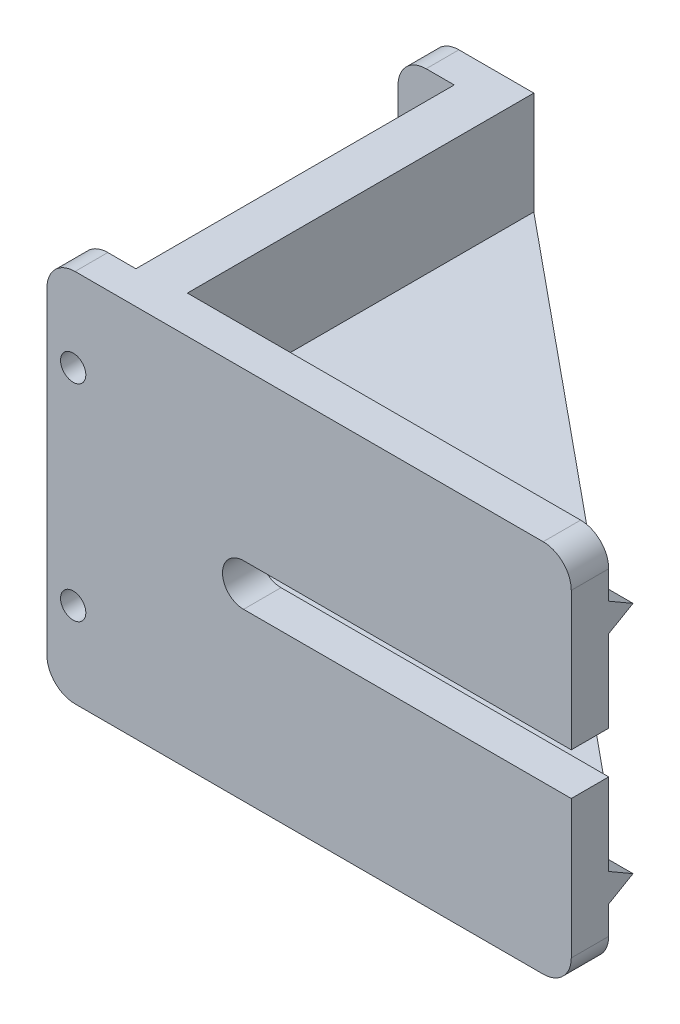
SolidWorks part; units mm, degrees
ref_plane "정면" through (0, 0, 0) normal (0, 0, 1) x (1, 0, 0)
ref_plane "윗면" through (0, 0, 0) normal (0, 1, 0) x (1, 0, 0)
ref_plane "우측면" through (0, 0, 0) normal (1, 0, 0) x (0, 0, -1)
sketch "스케치1" plane through (0, 0, 0) normal (1, 0, 0) x (0, 0, -1)
  line L1 (0, 0) -> (41, 0)
  line L2 (0, 0) -> (0, 40)
  line L3 (0, 40) -> (41, 40)
  line L4 (41, 0) -> (41, 40)
  dimension "D1" = 41
  dimension "D2" = 40
extrude "보스-돌출1" add sketch "스케치1" along normal blind 5
sketch "스케치2" plane through (0, 0, 0) normal (-1, 0, 0) x (0, 0, 1)
  line L0 (-41, 40) -> (0, 40) construction
  line L1 (-3.5, 40) -> (0, 40)
  line L2 (-3.5, 40) -> (-3.5, 0)
  line L3 (-3.5, 0) -> (0, 0)
  line L4 (0, 40) -> (0, 0)
  line L5 (-20.5, -5.7366) -> (-20.5, 42.7612) construction
  line L6 (-37.5, 0) -> (-41, 0)
  line L7 (-41, 40) -> (-41, 0)
  line L8 (-37.5, 40) -> (-41, 40)
  line L9 (-37.5, 40) -> (-37.5, 0)
  dimension "D1" = 3.5
extrude "보스-돌출2" add sketch "스케치2" along normal blind 6
sketch "스케치3" plane through (5, 0, 0) normal (1, 0, 0) x (0, 0, -1)
  line L0 (0, 0) -> (41, 0) construction
  line L1 (0, 40) -> (4, 40)
  line L2 (0, 40) -> (0, 0)
  line L3 (0, 0) -> (4, 0)
  line L4 (4, 40) -> (4, 34)
  line L5 (4, 34) -> (6.5981, 32.5)
  line L6 (4, 31) -> (6.5981, 32.5)
  line L7 (-6.5126, 20) -> (43.5218, 20) construction
  line L10 (4, 31) -> (4, 14)
  line L11 (4, 12) -> (4, 9)
  line L12 (4, 14) -> (4, 12)
  line L13 (4, 9) -> (6.5981, 7.5)
  line L14 (4, 6) -> (6.5981, 7.5)
  line L15 (4, 6) -> (4, 0)
  dimension "D1" = 4
  dimension "D2" = 6
  dimension "D3" = 60
  dimension "D4" = 60
  dimension "D5" = 3
  dimension "D6" = 40
extrude "보스-돌출3" add sketch "스케치3" along normal blind 45
sketch "스케치4" plane through (0, 0, -4) normal (0, 0, -1) x (-1, 0, 0)
  line L0 (-50, 9) -> (-50, 31) construction
  line L1 (-50, 29) -> (-5, 29)
  line L2 (-50, 29) -> (-50, 25)
  line L3 (-50, 25) -> (-5, 25)
  line L4 (-5, 29) -> (-5, 25)
  line L5 (-5, 9) -> (-5, 31) construction
  line L8 (-50, 40) -> (-5, 40) construction
  line L10 (-55.9639, 20) -> (9.4654, 20) construction
  line L11 (-50, 15) -> (-5, 15)
  line L12 (-5, 11) -> (-5, 15)
  line L13 (-50, 11) -> (-5, 11)
  line L14 (-50, 11) -> (-50, 15)
  dimension "D1" = 4
  dimension "D2" = 11
extrude "보스-돌출4" add sketch "스케치4" along normal blind 37
sketch "스케치5" plane through (0, 29, 0) normal (0, 1, 0) x (1, 0, 0)
  line L0 (50, 4) -> (5, 41)
  line L1 (5, 41) -> (50, 41)
  line L2 (50, 41) -> (50, 4)
extrude "컷-돌출1" cut sketch "스케치5" against normal blind 19
sketch "스케치6" plane through (0, 0, -41) normal (0, 0, -1) x (-1, 0, 0)
  line L2 (-5, 0) -> (6, 0) construction
  line L3 (6, 40) -> (6, 0) construction
  line L4 (-5, 40) -> (6, 40) construction
  circle A1 centre (3.2, 9) radius 1.35
  circle A2 centre (3.2, 31) radius 1.35
  point P10 (0, 0)
  dimension "D1" = 2.7
  dimension "D4" = 2.7
  dimension "D2" = 9
  dimension "D5" = 9
  dimension "D6" = 2.8
extrude "컷-돌출2" cut sketch "스케치6" against normal through all
fillet "필렛1" radius 3 2 edges at (50, 0, -2) (50, 40, -2)
fillet "필렛2" radius 3 4 edges at (-6, 0, -1.75) (-6, 0, -39.25) (-6, 40, -1.75) (-6, 40, -39.25)
sketch "스케치7" plane through (0, 0, -4) normal (0, 0, -1) x (-1, 0, 0)
  line L0 (-50, 15) -> (-50, 25) construction
  line L1 (-5, 15) -> (-5, 25) construction
  line L2 (-40, 22.25) -> (-15, 22.25)
  line L3 (-15, 17.75) -> (-40, 17.75)
  line L4 (-40, 22.25) -> (-50, 22.25)
  line L5 (-40, 17.75) -> (-50, 17.75)
  line L6 (-50, 17.75) -> (-50, 22.25)
  arc A1 (-15, 17.75) -> (-15, 22.25) centre (-15, 20) ccw
  dimension "D3" = 4.5
  dimension "D4" = 10
extrude "컷-돌출3" cut sketch "스케치7" against normal through all both and the other way through all
sketch "스케치8" plane through (0, 0, -41) normal (0, 0, -1) x (-1, 0, 0)
  circle A0 centre (-2.3, 31) radius 1.25
  circle A1 centre (-2.3, 9) radius 1.25
  circle A2 centre (3.2, 31) radius 1.35 construction
  point P6 (0, 0)
  dimension "D2" = 2.5
  dimension "D3" = 2.5
  dimension "D1" = 5.5
extrude "컷-돌출4" cut sketch "스케치8" against normal blind 5
